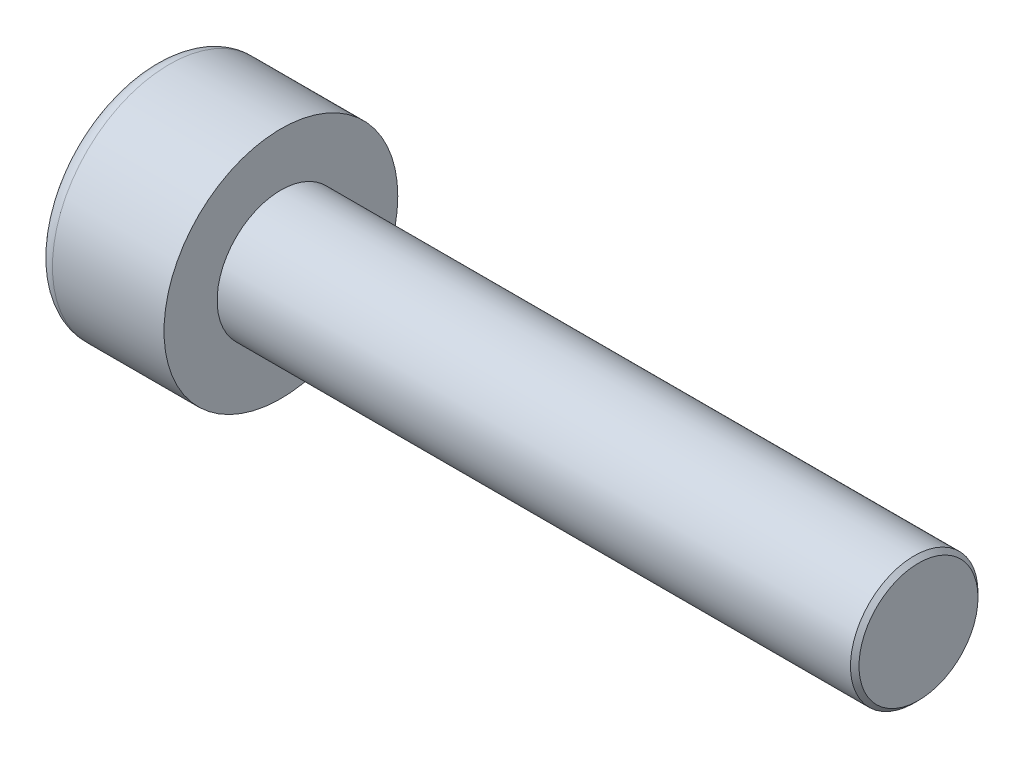
SolidWorks part; units mm, degrees
ref_plane "Front" through (0, 0, 0) normal (0, 0, 1) x (1, 0, 0)
ref_plane "Top" through (0, 0, 0) normal (0, 1, 0) x (1, 0, 0)
ref_plane "Right" through (0, 0, 0) normal (1, 0, 0) x (0, 0, -1)
sketch "Sketch1" plane through (0, 0, 0) normal (1, 0, 0) x (0, 0, -1)
  circle A0 centre (0, 0) radius 2.75
  dimension "dk" = 5.5
extrude "BaseHead" add sketch "Sketch1" along normal blind 3
sketch "Sketch2" plane through (3, 0, 0) normal (1, 0, 0) x (0, 0, -1)
  circle A0 centre (0, 0) radius 1.5
  dimension "d" = 3
extrude "BaseBody" add sketch "Sketch2" along normal blind 15
cosmetic thread "ThreadCosmetic1" parameters "b"=10, "D2"=2.459
sketch "Sketch3" plane through (0, 0, 0) normal (1, 0, 0) x (0, 0, -1)
  line L1 (1.4434, 0) -> (0.7217, 1.25)
  line L2 (0.7217, 1.25) -> (-0.7217, 1.25)
  line L3 (-0.7217, 1.25) -> (-1.4434, 0)
  line L4 (-1.4434, 0) -> (-0.7217, -1.25)
  line L5 (-0.7217, -1.25) -> (0.7217, -1.25)
  line L6 (0.7217, -1.25) -> (1.4434, 0)
  circle A0 centre (0, 0) radius 1.25 construction
  dimension "s" = 2.5
  dimension "e" = 2.8868
extrude "HexagonSocket" cut sketch "Sketch3" along normal blind 1.3
sketch "Sketch4" plane through (-4.1961, 0.75, 0) normal (0, 0, 1) x (-1, 0, 0)
  line L0 (-5.4961, 2) -> (-6.2178, 0.75)
  line L2 (-6.2178, 0.75) -> (-5.4961, 0.75)
  line L3 (-5.4961, 0.75) -> (-5.4961, 2)
  line L4 (-5.0351, 0.75) -> (0.839, 0.75) construction
  line L5 (-22.1961, 0.75) -> (-7.1961, 0.75) construction
  line L6 (-7.1961, 0.75) -> (-4.1961, 0.75) construction
  dimension "m" = 60
revolve "Cut-Revolve1" cut sketch "Sketch4" angle 360 about L4
fillet "HeadFillet" [suppressed] radius 0.1
fillet "TopFillet" radius 0.375 1 edges at (0, 0, -2.75)
chamfer "Chamfer1" distance 0.1 angle 45 1 edges at (18, 0, -1.5)
sketch "Sketch5" plane through (0, 0, 0) normal (0, 0, 1) x (1, 0, 0)
  line L0 (17.9, 1.2657) -> (18.0352, 1.5)
  line L1 (18.0352, 1.5) -> (18.0352, 1.7705)
  line L2 (18.0352, 1.7705) -> (17.7647, 1.7705)
  line L3 (17.7647, 1.7705) -> (17.7647, 1.5)
  line L4 (17.7647, 1.5) -> (17.9, 1.2657)
  line L5 (0, 0) -> (7.8886, 0) construction
  line L6 (17.9, -1.5) -> (17.9, 1.5) construction
  dimension "D1" = 3
  dimension "D2" = 0.2705
revolve "Cut-Revolve10" [suppressed] cut sketch "Sketch5" angle 360 about L5
pattern_linear "LPattern10" [suppressed] count 31 spacing 0.3246 along (1, 0, 0)
equation "\"r1@TopFillet\" = \"d@Sketch2\" / 8"
equation "\"D1@Chamfer1\" = \"r@HeadFillet\""
equation "\"D1@Sketch5\" = \"d@Sketch2\""
equation "\"D2@Sketch5\" =  ( \"d@Sketch2\" - \"D2@ThreadCosmetic1\" )  / 2"
equation "\"D3@LPattern10\" = \"D2@Sketch5\" * 1.2"
equation "\"D1@LPattern10\" = \"b@ThreadCosmetic1\" / \"D3@LPattern10\""
